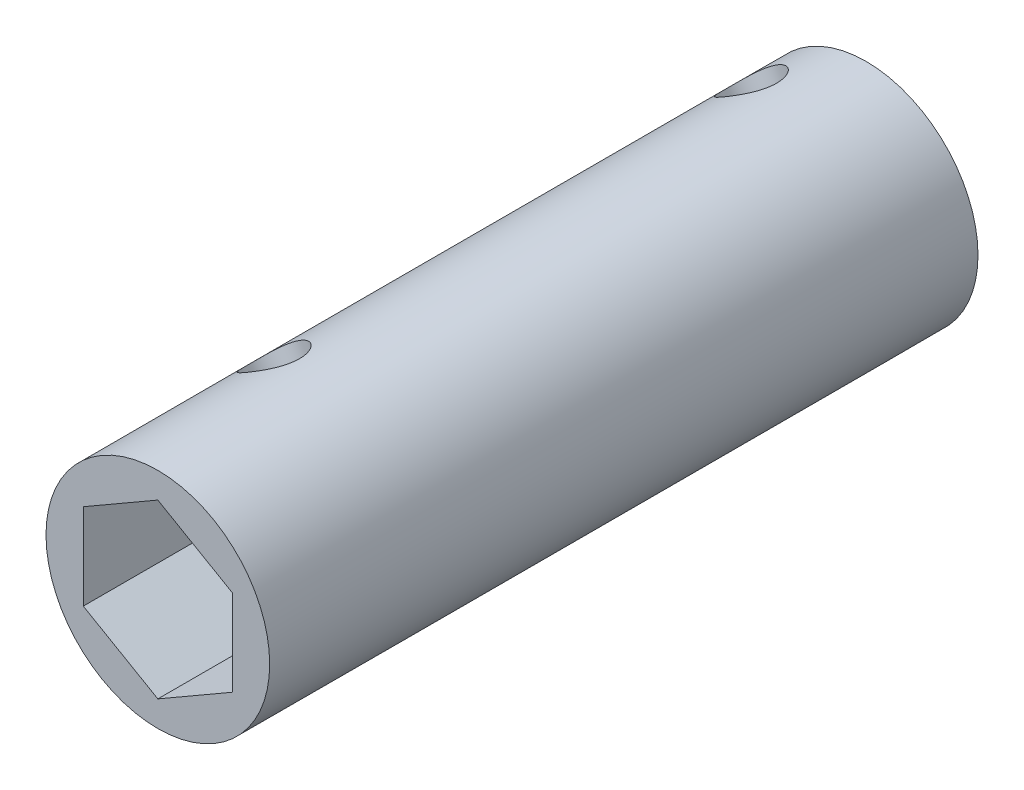
SolidWorks part; units mm, degrees
material "6061-T6 (SS)"
ref_plane "Front" through (0, 0, 0) normal (0, 0, 1) x (1, 0, 0)
ref_plane "Top" through (0, 0, 0) normal (0, 1, 0) x (1, 0, 0)
ref_plane "Right" through (0, 0, 0) normal (1, 0, 0) x (0, 0, -1)
sketch "Sketch1" plane through (0, 0, 0) normal (0, 0, 1) x (1, 0, 0)
  line L1 (6.35, 3.6662) -> (0, 7.3323)
  line L2 (0, 7.3323) -> (-6.35, 3.6662)
  line L3 (-6.35, 3.6662) -> (-6.35, -3.6662)
  line L4 (-6.35, -3.6662) -> (0, -7.3323)
  line L5 (0, -7.3323) -> (6.35, -3.6662)
  line L6 (6.35, -3.6662) -> (6.35, 3.6662)
  circle A0 centre (0, 0) radius 6.35 construction
  circle A1 centre (0, 0) radius 9.525
  dimension "D2" = 19.05
  dimension "D1" = 12.7
extrude "Boss-Extrude1" add sketch "Sketch1" along normal blind 60.325
ref_plane "Plane1" through (5.08, -8.7988, 0) normal (-0.5, 0.866, 0) x (0.866, 0.5, 0)
sketch "Sketch3" plane through (5.08, -8.7988, 0) normal (-0.5, 0.866, 0) x (0.866, 0.5, 0)
  line L0 (3.6662, 0) -> (-3.6662, 0) construction
  circle A0 centre (0, -5.08) radius 2.3813
  circle A1 centre (0, -45.72) radius 2.3812
  dimension "D1" = 5.08
  dimension "D3" = 4.7625
  dimension "D2" = 45.72
extrude "Cut-Extrude1" cut sketch "Sketch3" against normal through all both and the other way through all
